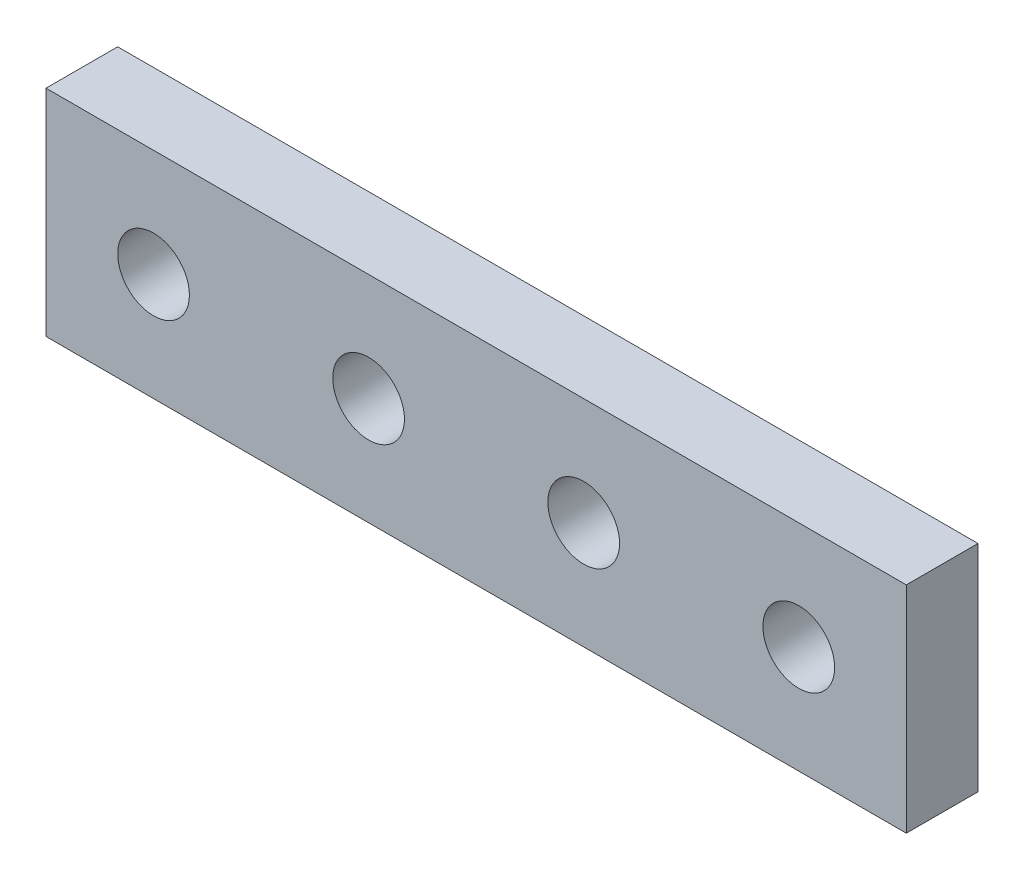
SolidWorks part; units mm, degrees
ref_plane "Front Plane" through (0, 0, 0) normal (0, 0, 1) x (1, 0, 0)
ref_plane "Top Plane" through (0, 0, 0) normal (0, 1, 0) x (1, 0, 0)
ref_plane "Right Plane" through (0, 0, 0) normal (1, 0, 0) x (0, 0, -1)
sketch "Sketch1" plane through (0, 0, 0) normal (0, 0, 1) x (1, 0, 0)
  line L0 (0, 0) -> (120, 0)
  line L1 (120, 0) -> (120, 30)
  line L2 (120, 30) -> (0, 30)
  line L3 (0, 30) -> (0, 0)
  circle A0 centre (15, 15) radius 5
  circle A2 centre (45, 15) radius 5
  circle A3 centre (75, 15) radius 5
  circle A4 centre (105, 15) radius 5
  dimension "D4" = 10
  dimension "D7" = 30
  dimension "D1" = 120
  dimension "D2" = 30
  dimension "D3" = 15
  dimension "D5" = 15
  dimension "D6" = 4
extrude "Boss-Extrude1" add sketch "Sketch1" along normal blind 10
